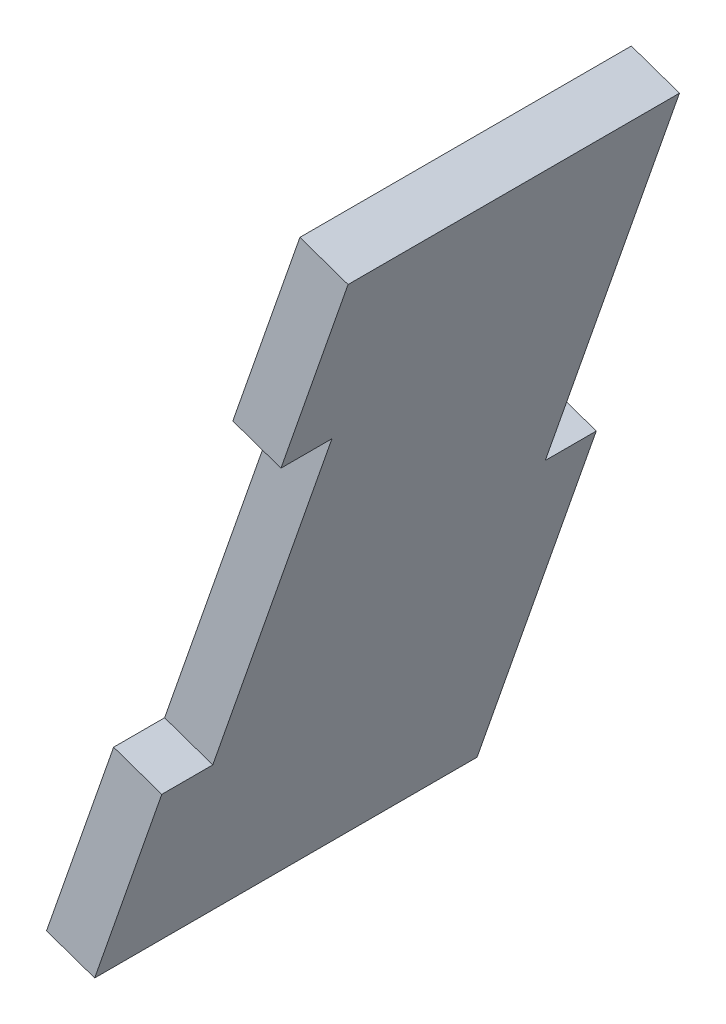
SolidWorks part; units mm, degrees
ref_plane "Front Plane" through (0, 0, 0) normal (0, 0, 1) x (1, 0, 0)
ref_plane "Top Plane" through (0, 0, 0) normal (0, 1, 0) x (1, 0, 0)
ref_plane "Right Plane" through (0, 0, 0) normal (1, 0, 0) x (0, 0, -1)
sketch "Sketch1" plane through (0, 0, 0) normal (0, 0, 1) x (1, 0, 0)
  line L0 (322.6658, 315.3883) -> (306.887, 270.1011)
  line L1 (309.8853, 269.0565) -> (325.6641, 314.3437)
  line L2 (325.6641, 314.3437) -> (322.6658, 315.3883)
  line L3 (309.8853, 269.0565) -> (306.887, 270.1011)
  dimension "D1" = 3.175
extrude "Boss-Extrude1" add sketch "Sketch1" against normal up to surface (23.8125 mm away) contours L1 L2 L0 L3
sketch "Sketch2" plane through (192.7437, -67.155, 0) normal (0.9443, -0.329, 0) x (0, 0, -1)
  line L0 (20.6375, 477.2227) -> (20.6375, 375.1205) construction
  line L1 (23.8125, 403.9915) -> (20.6375, 403.9915)
  line L2 (23.8125, 403.9915) -> (23.8125, 378.5915)
  line L3 (23.8125, 378.5915) -> (20.6375, 378.5915)
  line L4 (20.6375, 403.9915) -> (20.6375, 378.5915)
  line L5 (0, 356.0342) -> (0, 403.9915) construction
  line L6 (0, 391.2915) -> (3.175, 391.2915)
  line L7 (0, 391.2915) -> (0, 368.7342)
  line L8 (0, 368.7342) -> (3.175, 368.7342)
  line L9 (3.175, 391.2915) -> (3.175, 368.7342)
  line L10 (3.175, 317.4418) -> (3.175, 322.8859) construction
  line L11 (23.8125, 403.9915) -> (0, 403.9915) construction
  line L12 (23.8125, 356.0342) -> (0, 356.0342) construction
  dimension "D1" = 12.7
  dimension "D2" = 12.7
  dimension "D3" = 25.4
extrude "Cut-Extrude1" cut sketch "Sketch2" against normal blind 3.175
